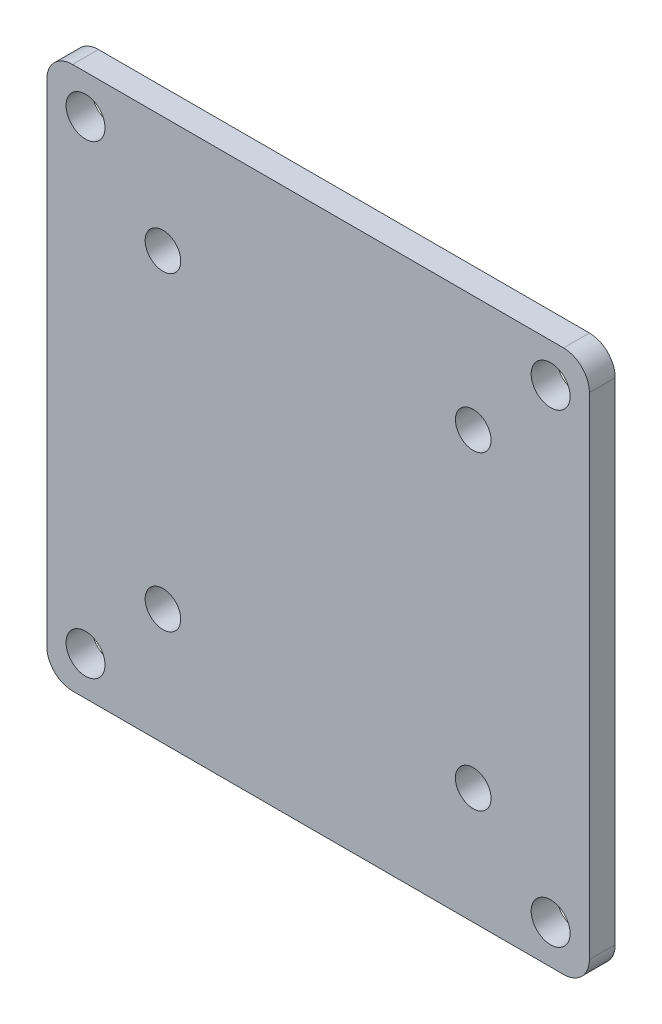
SolidWorks part; units mm, degrees
ref_plane "Front Plane" through (0, 0, 0) normal (1, 0, 0) x (0, 1, 0)
ref_plane "Top Plane" through (0, 0, 0) normal (0, 0, 1) x (0, 1, 0)
ref_plane "Right Plane" through (0, 0, 0) normal (0, 1, 0) x (-1, 0, 0)
sketch "Sketch1" plane through (0, 0, 0) normal (0, 0, 1) x (0, 1, 0)
  line L1 (26.67, -26.67) -> (-26.67, -26.67)
  line L2 (26.67, -26.67) -> (26.67, 26.67)
  line L3 (26.67, 26.67) -> (-26.67, 26.67)
  line L4 (-26.67, -26.67) -> (-26.67, 26.67)
  line L5 (26.67, -26.67) -> (-26.67, 26.67) construction
  line L6 (26.67, 26.67) -> (-26.67, -26.67) construction
  line L7 (22.86, -22.86) -> (-22.86, -22.86) construction
  line L8 (22.86, -22.86) -> (22.86, 22.86) construction
  line L9 (22.86, 22.86) -> (-22.86, 22.86) construction
  line L10 (-22.86, -22.86) -> (-22.86, 22.86) construction
  line L11 (22.86, -22.86) -> (-22.86, 22.86) construction
  line L12 (22.86, 22.86) -> (-22.86, -22.86) construction
  line L13 (15.25, -15.25) -> (-15.25, -15.25) construction
  line L14 (15.25, -15.25) -> (15.25, 15.25) construction
  line L15 (15.25, 15.25) -> (-15.25, 15.25) construction
  line L16 (-15.25, -15.25) -> (-15.25, 15.25) construction
  line L17 (15.25, -15.25) -> (-15.25, 15.25) construction
  line L18 (15.25, 15.25) -> (-15.25, -15.25) construction
  circle A0 centre (-22.86, -22.86) radius 1.9145
  circle A1 centre (22.86, -22.86) radius 1.9145
  circle A2 centre (22.86, 22.86) radius 1.9145
  circle A3 centre (-22.86, 22.86) radius 1.9145
  circle A4 centre (-15.25, 15.25) radius 1.75
  circle A5 centre (15.25, 15.25) radius 1.75
  circle A6 centre (15.25, -15.25) radius 1.75
  circle A7 centre (-15.25, -15.25) radius 1.75
  point P0 (0, 0)
  point P6 (0, 0)
  point P15 (0, 0)
  dimension "D5" = 3.829
  dimension "D7" = 3.5
  dimension "D1" = 53.34
  dimension "D3" = 45.72
  dimension "D4" = 45.72
  dimension "D6" = 30.5
extrude "Boss-Extrude1" add sketch "Sketch1" along normal blind 2.54
fillet "Fillet1" radius 2.54 4 edges at (26.67, -26.67, 1.27) (-26.67, -26.67, 1.27) (-26.67, 26.67, 1.27) (26.67, 26.67, 1.27)
equation "\"Perf_Board_Radius\"= 0.125in"
equation "\"D5@Sketch1\" = \"Perf_Board_Radius\" + \"Tolerance\" + .01in"
equation "\"ESC Mounting Radius\"= 3.1"
equation "\"D7@Sketch1\"= \"ESC Mounting Radius\" + \"Tolerance\""
equation "\"Tolerance\"= .4mm"
